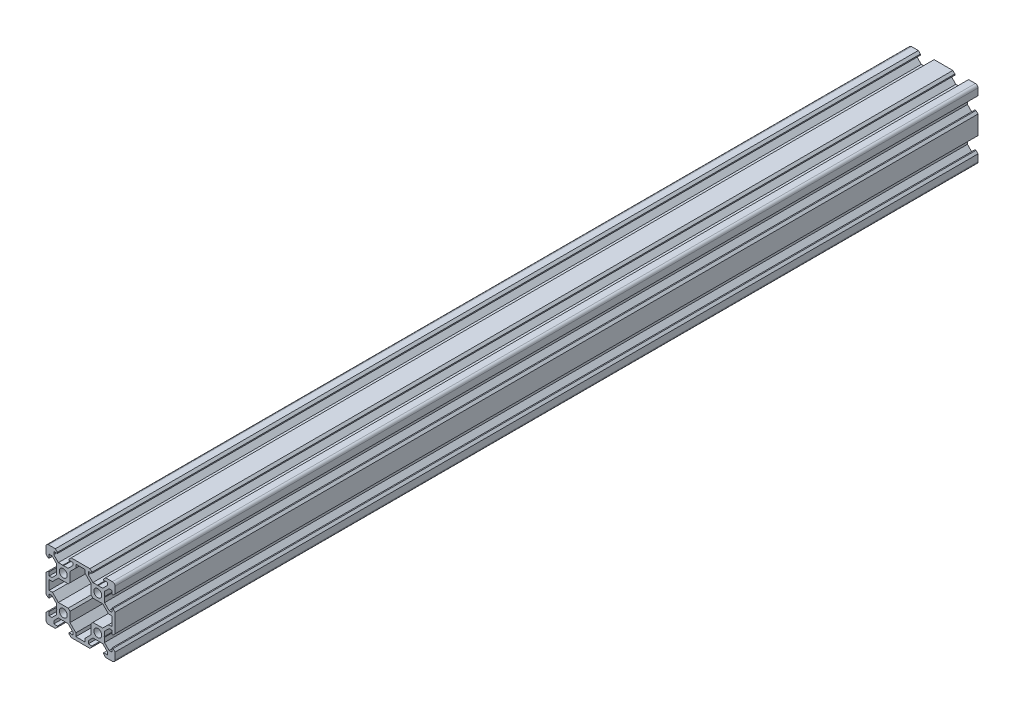
SolidWorks part; units mm, degrees
ref_plane "Front Plane" through (0, 0, 0) normal (0, 0, 1) x (1, 0, 0)
ref_plane "Top Plane" through (0, 0, 0) normal (0, 1, 0) x (1, 0, 0)
ref_plane "Right Plane" through (0, 0, 0) normal (1, 0, 0) x (0, 0, -1)
sketch "Sketch1" plane through (0, 0, 0) normal (0, 0, 1) x (1, 0, 0)
  line L0 (0, 18.2) -> (0, -18.2) construction
  line B0 (13.69, -10) -> (13.9, -10.21)
  line B1 (13.9, -10.21) -> (13.9, -12.8393)
  line B2 (13.9, -12.8393) -> (16.5607, -15.5)
  line B3 (16.5607, -15.5) -> (18.2, -15.5)
  line B4 (18.2, -15.5) -> (18.2, -13.395)
  line B5 (18.2, -13.395) -> (18.815, -13.395)
  line B6 (18.815, -13.395) -> (20, -14.58)
  line B7 (20, -18.5) -> (20, -14.58)
  arc B8 (18.5, -20) -> (20, -18.5) centre (18.5, -18.5) ccw
  line B9 (18.5, -20) -> (14.58, -20)
  line B10 (13.395, -18.815) -> (14.58, -20)
  line B11 (13.395, -18.2) -> (13.395, -18.815)
  line B12 (15.5, -18.2) -> (13.395, -18.2)
  line B13 (15.5, -16.5607) -> (15.5, -18.2)
  line B14 (12.8393, -13.9) -> (15.5, -16.5607)
  line B15 (10.21, -13.9) -> (12.8393, -13.9)
  line B16 (10, -13.69) -> (10.21, -13.9)
  line B17 (10, -13.69) -> (9.79, -13.9)
  line B18 (9.79, -13.9) -> (7.1607, -13.9)
  line B19 (7.1607, -13.9) -> (4.5, -16.5607)
  line B20 (4.5, -16.5607) -> (4.5, -18.2)
  line B21 (4.5, -18.2) -> (6.605, -18.2)
  line B22 (6.605, -18.2) -> (6.605, -18.815)
  line B23 (6.605, -18.815) -> (5.42, -20)
  line B24 (5.42, -20) -> (-5.42, -20)
  line B25 (-6.605, -18.815) -> (-5.42, -20)
  line B26 (-6.605, -18.2) -> (-6.605, -18.815)
  line B27 (-4.5, -18.2) -> (-6.605, -18.2)
  line B28 (-4.5, -16.5607) -> (-4.5, -18.2)
  line B29 (-7.1607, -13.9) -> (-4.5, -16.5607)
  line B30 (-9.79, -13.9) -> (-7.1607, -13.9)
  line B31 (-10, -13.69) -> (-9.79, -13.9)
  line B32 (-10, -13.69) -> (-10.21, -13.9)
  line B33 (-10.21, -13.9) -> (-12.8393, -13.9)
  line B34 (-12.8393, -13.9) -> (-15.5, -16.5607)
  line B35 (-15.5, -16.5607) -> (-15.5, -18.2)
  line B36 (-15.5, -18.2) -> (-13.395, -18.2)
  line B37 (-13.395, -18.2) -> (-13.395, -18.815)
  line B38 (-13.395, -18.815) -> (-14.58, -20)
  line B39 (-14.58, -20) -> (-18.5, -20)
  arc B40 (-20, -18.5) -> (-18.5, -20) centre (-18.5, -18.5) ccw
  line B41 (-20, -18.5) -> (-20, -14.58)
  line B42 (-18.815, -13.395) -> (-20, -14.58)
  line B43 (-18.2, -13.395) -> (-18.815, -13.395)
  line B44 (-18.2, -15.5) -> (-18.2, -13.395)
  line B45 (-16.5607, -15.5) -> (-18.2, -15.5)
  line B46 (-13.9, -12.8393) -> (-16.5607, -15.5)
  line B47 (-13.9, -10.21) -> (-13.9, -12.8393)
  line B48 (-13.69, -10) -> (-13.9, -10.21)
  line B49 (-13.69, -10) -> (-13.9, -9.79)
  line B50 (-13.9, -9.79) -> (-13.9, -7.1607)
  line B51 (-13.9, -7.1607) -> (-16.5607, -4.5)
  line B52 (-16.5607, -4.5) -> (-18.2, -4.5)
  line B53 (-18.2, -4.5) -> (-18.2, -6.605)
  line B54 (-18.2, -6.605) -> (-18.815, -6.605)
  line B55 (-18.815, -6.605) -> (-20, -5.42)
  line B56 (-20, -5.42) -> (-20, 5.42)
  line B57 (-18.815, 6.605) -> (-20, 5.42)
  line B58 (-18.2, 6.605) -> (-18.815, 6.605)
  line B59 (-18.2, 4.5) -> (-18.2, 6.605)
  line B60 (-16.5607, 4.5) -> (-18.2, 4.5)
  line B61 (-13.9, 7.1607) -> (-16.5607, 4.5)
  line B62 (-13.9, 9.79) -> (-13.9, 7.1607)
  line B63 (-13.69, 10) -> (-13.9, 9.79)
  line B64 (-13.69, 10) -> (-13.9, 10.21)
  line B65 (-13.9, 10.21) -> (-13.9, 12.8393)
  line B66 (-13.9, 12.8393) -> (-16.5607, 15.5)
  line B67 (-16.5607, 15.5) -> (-18.2, 15.5)
  line B68 (-18.2, 15.5) -> (-18.2, 13.395)
  line B69 (-18.2, 13.395) -> (-18.815, 13.395)
  line B70 (-18.815, 13.395) -> (-20, 14.58)
  line B71 (-20, 14.58) -> (-20, 18.5)
  arc B72 (-18.5, 20) -> (-20, 18.5) centre (-18.5, 18.5) ccw
  line B73 (-14.58, 20) -> (-18.5, 20)
  line B74 (-13.395, 18.815) -> (-14.58, 20)
  line B75 (-13.395, 18.2) -> (-13.395, 18.815)
  line B76 (-15.5, 18.2) -> (-13.395, 18.2)
  line B77 (-15.5, 16.5607) -> (-15.5, 18.2)
  line B78 (-12.8393, 13.9) -> (-15.5, 16.5607)
  line B79 (-10.21, 13.9) -> (-12.8393, 13.9)
  line B80 (-10, 13.69) -> (-10.21, 13.9)
  line B81 (-10, 13.69) -> (-9.79, 13.9)
  line B82 (-9.79, 13.9) -> (-7.1607, 13.9)
  line B83 (-7.1607, 13.9) -> (-4.5, 16.5607)
  line B84 (-4.5, 16.5607) -> (-4.5, 18.2)
  line B85 (-4.5, 18.2) -> (-6.605, 18.2)
  line B86 (-6.605, 18.2) -> (-6.605, 18.815)
  line B87 (-6.605, 18.815) -> (-5.42, 20)
  line B88 (5.42, 20) -> (-5.42, 20)
  line B89 (6.605, 18.815) -> (5.42, 20)
  line B90 (6.605, 18.2) -> (6.605, 18.815)
  line B91 (4.5, 18.2) -> (6.605, 18.2)
  line B92 (4.5, 16.5607) -> (4.5, 18.2)
  line B93 (7.1607, 13.9) -> (4.5, 16.5607)
  line B94 (9.79, 13.9) -> (7.1607, 13.9)
  line B95 (10, 13.69) -> (9.79, 13.9)
  line B96 (10, 13.69) -> (10.21, 13.9)
  line B97 (10.21, 13.9) -> (12.8393, 13.9)
  line B98 (12.8393, 13.9) -> (15.5, 16.5607)
  line B99 (15.5, 16.5607) -> (15.5, 18.2)
  line B100 (15.5, 18.2) -> (13.395, 18.2)
  line B101 (13.395, 18.2) -> (13.395, 18.815)
  line B102 (13.395, 18.815) -> (14.58, 20)
  line B103 (18.5, 20) -> (14.58, 20)
  arc B104 (20, 18.5) -> (18.5, 20) centre (18.5, 18.5) ccw
  line B105 (20, 14.58) -> (20, 18.5)
  line B106 (18.815, 13.395) -> (20, 14.58)
  line B107 (18.2, 13.395) -> (18.815, 13.395)
  line B108 (18.2, 15.5) -> (18.2, 13.395)
  line B109 (16.5607, 15.5) -> (18.2, 15.5)
  line B110 (13.9, 12.8393) -> (16.5607, 15.5)
  line B111 (13.9, 10.21) -> (13.9, 12.8393)
  line B112 (13.69, 10) -> (13.9, 10.21)
  line B113 (13.69, 10) -> (13.9, 9.79)
  line B114 (13.9, 9.79) -> (13.9, 7.1607)
  line B115 (13.9, 7.1607) -> (16.5607, 4.5)
  line B116 (16.5607, 4.5) -> (18.2, 4.5)
  line B117 (18.2, 4.5) -> (18.2, 6.605)
  line B118 (18.2, 6.605) -> (18.815, 6.605)
  line B119 (18.815, 6.605) -> (20, 5.42)
  line B120 (20, -5.42) -> (20, 5.42)
  line B121 (18.815, -6.605) -> (20, -5.42)
  line B122 (18.2, -6.605) -> (18.815, -6.605)
  line B123 (18.2, -4.5) -> (18.2, -6.605)
  line B124 (16.5607, -4.5) -> (18.2, -4.5)
  line B125 (13.9, -7.1607) -> (16.5607, -4.5)
  line B126 (13.9, -9.79) -> (13.9, -7.1607)
  line B127 (13.69, -10) -> (13.9, -9.79)
  circle B128 centre (-10, -10) radius 2.3
  circle B129 centre (10, 10) radius 2.3
  circle B130 centre (-10, 10) radius 2.3
  circle B131 centre (10, -10) radius 2.3
  line B132 (-6.1, -12.8393) -> (-6.1, -7.1607)
  line B133 (-6.1, -7.1607) -> (-7.1607, -6.1)
  line B134 (-12.8393, -6.1) -> (-7.1607, -6.1)
  line B135 (-16.2393, -2.7) -> (-12.8393, -6.1)
  line B136 (-18.2, -2.7) -> (-16.2393, -2.7)
  line B137 (-18.2, -2.7) -> (-18.2, 2.7)
  line B138 (-18.2, 2.7) -> (-16.2393, 2.7)
  line B139 (-16.2393, 2.7) -> (-12.8393, 6.1)
  line B140 (-12.8393, 6.1) -> (-7.1607, 6.1)
  line B141 (-7.1607, 6.1) -> (-6.1, 7.1607)
  line B142 (-6.1, 12.8393) -> (-6.1, 7.1607)
  line B143 (-2.7, 16.2393) -> (-6.1, 12.8393)
  line B144 (-2.7, 18.2) -> (-2.7, 16.2393)
  line B145 (2.7, 18.2) -> (-2.7, 18.2)
  line B146 (2.7, 18.2) -> (2.7, 16.2393)
  line B147 (2.7, 16.2393) -> (6.1, 12.8393)
  line B148 (6.1, 12.8393) -> (6.1, 7.1607)
  line B149 (6.1, 7.1607) -> (7.1607, 6.1)
  line B150 (12.8393, 6.1) -> (7.1607, 6.1)
  line B151 (16.2393, 2.7) -> (12.8393, 6.1)
  line B152 (18.2, 2.7) -> (16.2393, 2.7)
  line B153 (18.2, -2.7) -> (18.2, 2.7)
  line B154 (18.2, -2.7) -> (16.2393, -2.7)
  line B155 (16.2393, -2.7) -> (12.8393, -6.1)
  line B156 (12.8393, -6.1) -> (7.1607, -6.1)
  line B157 (7.1607, -6.1) -> (6.1, -7.1607)
  line B158 (6.1, -12.8393) -> (6.1, -7.1607)
  line B159 (2.7, -16.2393) -> (6.1, -12.8393)
  line B160 (2.7, -18.2) -> (2.7, -16.2393)
  line B161 (2.7, -18.2) -> (-2.7, -18.2)
  line B162 (-2.7, -18.2) -> (-2.7, -16.2393)
  line B163 (-2.7, -16.2393) -> (-6.1, -12.8393)
sketch_block_instance "S6-8080 - V-Slot-1"
sketch_block "S6-8080 - V-Slot"
extrude "Boss-Extrude1" add sketch "Sketch1" along normal blind 500
